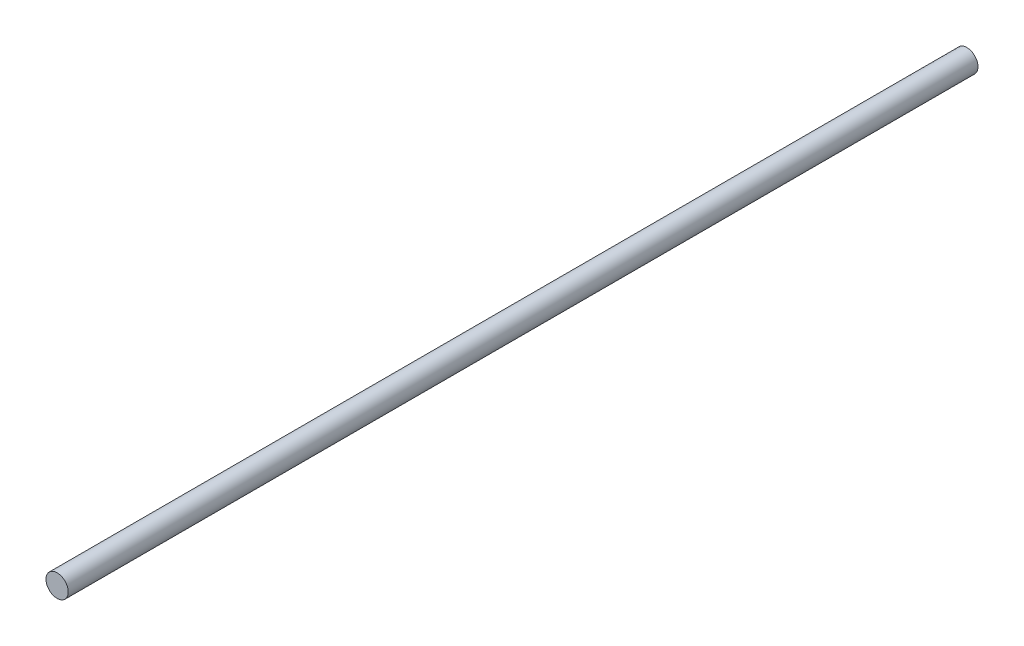
SolidWorks part; units mm, degrees
ref_plane "Front Plane" through (0, 0, 0) normal (0, 0, 1) x (1, 0, 0)
ref_plane "Top Plane" through (0, 0, 0) normal (0, 1, 0) x (1, 0, 0)
ref_plane "Right Plane" through (0, 0, 0) normal (1, 0, 0) x (0, 0, -1)
sketch "Sketch1" plane through (0, 0, 0) normal (0, 0, 1) x (1, 0, 0)
  circle A0 centre (0, 0) radius 4
extrude "Boss-Extrude1" add sketch "Sketch1" along normal mid plane 327
